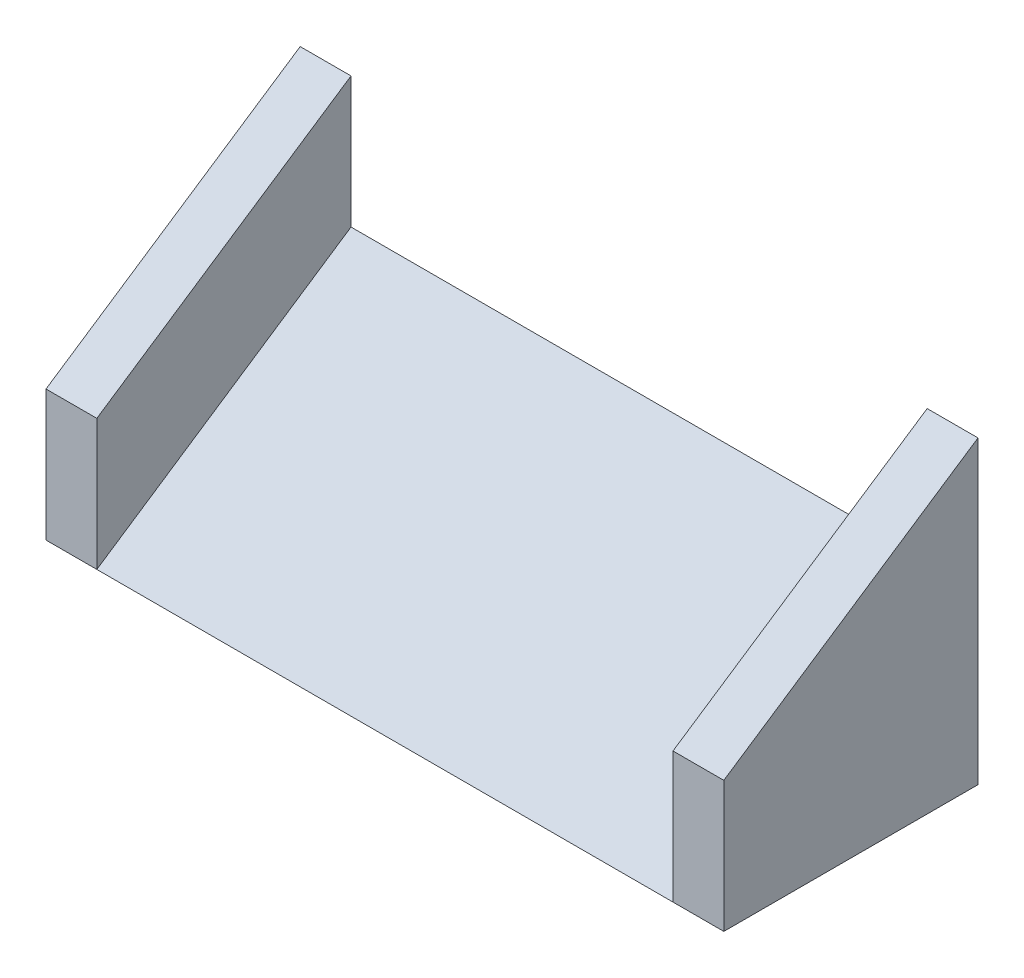
SolidWorks part; units mm, degrees
ref_plane "Plano frontal" through (0, 0, 0) normal (0, 0, 1) x (1, 0, 0)
ref_plane "Plano superior" through (0, 0, 0) normal (0, 1, 0) x (1, 0, 0)
ref_plane "Plano direito" through (0, 0, 0) normal (1, 0, 0) x (0, 0, -1)
sketch "Sketch1" plane through (0, 0, 0) normal (1, 0, 0) x (0, 0, -1)
  line L0 (-7.5, -5) -> (7.5, -5)
  line L5 (7.5, -5) -> (7.5, 5)
  line L6 (7.5, 5) -> (-7.5, -5)
  point P4 (0, -5)
  point P5 (7.5, 0)
  dimension "D1" = 15
  dimension "D2" = 10
  dimension "D3" = 33.69
extrude "Boss-Extrude1" add sketch "Sketch1" along normal mid plane 34
sketch "Sketch2" plane through (17, 0, 0) normal (1, 0, 0) x (0, 0, -1)
  line L0 (-7.5, -5) -> (-7.5, 2.7226)
  line L1 (7.5, -5) -> (7.5, 12.7226)
  line L2 (-7.5, -5) -> (7.5, -5)
  line L3 (-7.5, 2.7226) -> (7.5, 12.7226)
  line L4 (7.5, 5) -> (-7.5, -5) construction
extrude "Boss-Extrude2" add sketch "Sketch2" along normal blind 3
mirror "Mirror1" about plane through (0, 0, 0) normal (1, 0, 0) of "Boss-Extrude2"
